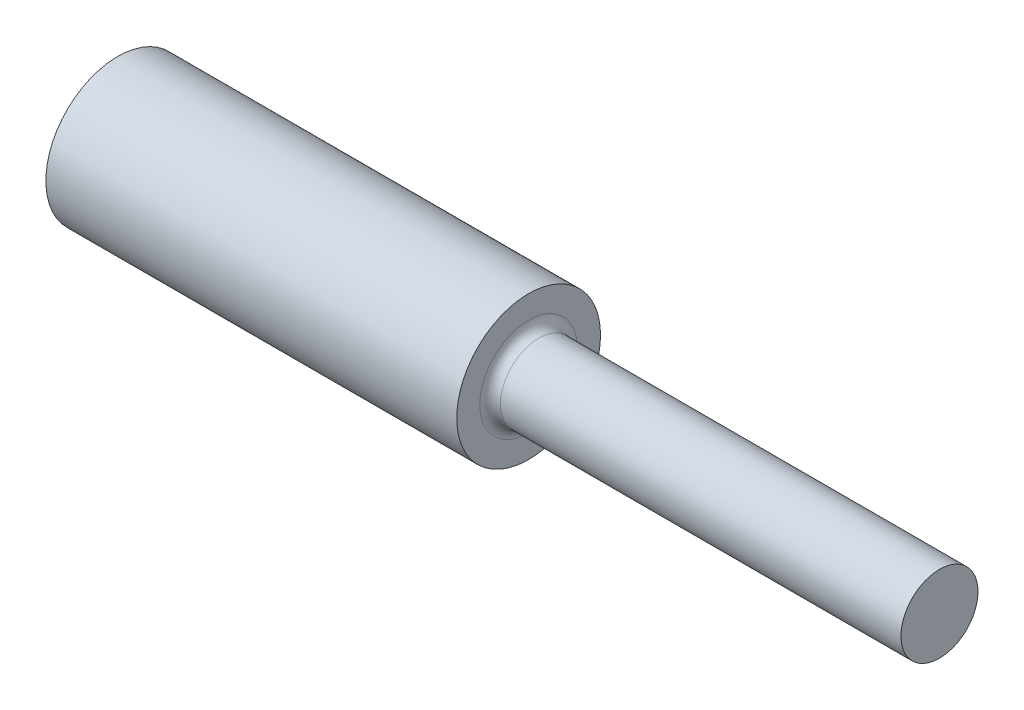
SolidWorks part; units mm, degrees
material "Gray Cast Iron"
ref_plane "Front Plane" through (0, 0, 0) normal (0, 0, 1) x (1, 0, 0)
ref_plane "Top Plane" through (0, 0, 0) normal (0, 1, 0) x (1, 0, 0)
ref_plane "Right Plane" through (0, 0, 0) normal (1, 0, 0) x (0, 0, -1)
sketch "Sketch3" plane through (0, 0, 0) normal (0, 0, -1) x (-1, 0, 0)
  line L0 (-60.4108, 0) -> (165.7063, 0) construction
  line L1 (-101.6, 0) -> (-101.6, 9.525)
  line L2 (-101.6, 9.525) -> (0, 9.525)
  line L3 (0, 9.525) -> (0, 17.78)
  line L4 (0, 17.78) -> (101.6, 17.78)
  line L5 (101.6, 17.78) -> (101.6, 0)
  line L6 (101.6, 0) -> (-101.6, 0)
  dimension "D1" = 101.6
  dimension "D2" = 101.6
  dimension "D3" = 35.56
  dimension "D4" = 19.05
revolve "Revolve1" add sketch "Sketch3" angle 360 about L0
fillet "Fillet2" radius 2.54 1 edges at (0, 0, -9.525)
sketch "Sketch4" plane through (0, 0, 0) normal (0, 0, 1) x (1, 0, 0)
  line L0 (19.05, 25.9802) -> (19.05, -25.8728)
  line L1 (0, -17.78) -> (0, 17.78) construction
  dimension "D1" = 19.05
